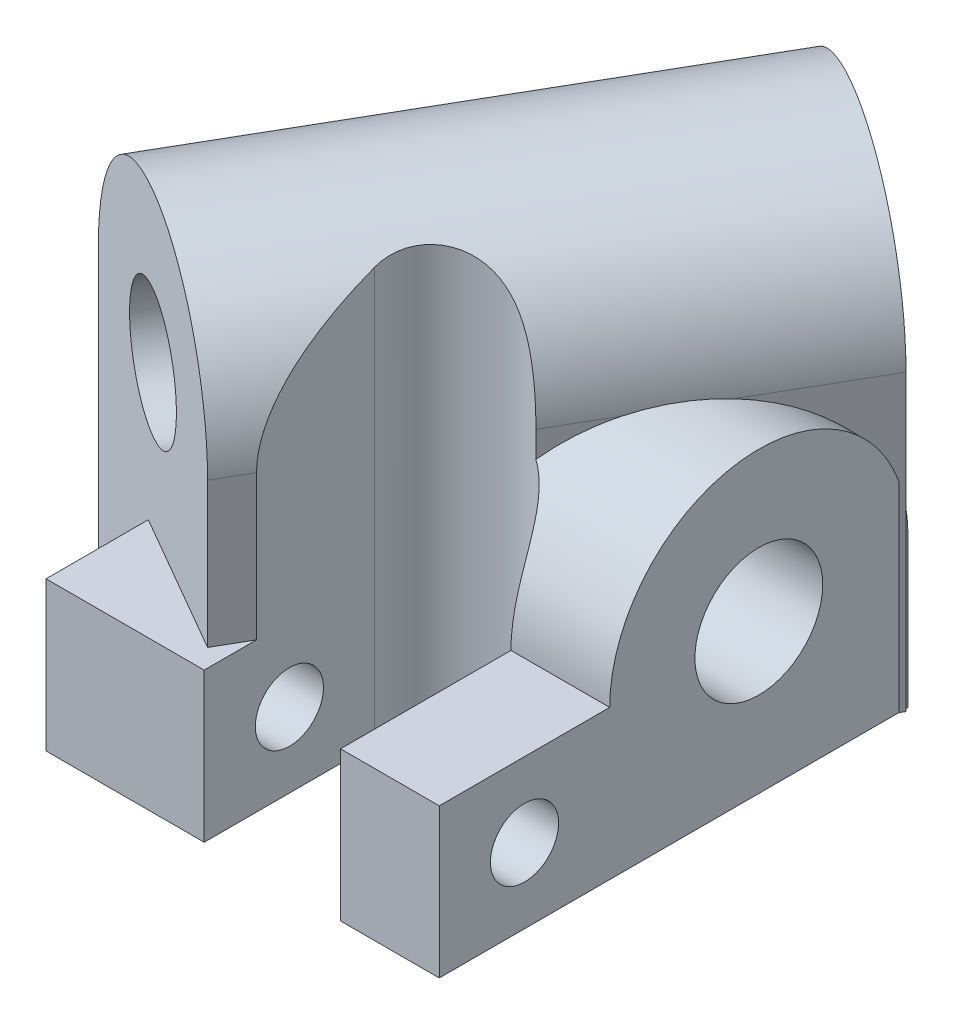
SolidWorks part; units mm, degrees
ref_plane "Front Plane" through (0, 0, 0) normal (0, 0, 1) x (1, 0, 0)
ref_plane "Top Plane" through (0, 0, 0) normal (0, 1, 0) x (1, 0, 0)
ref_plane "Right Plane" through (0, 0, 0) normal (1, 0, 0) x (0, 0, -1)
sketch "Sketch1" plane through (0, 0, 0) normal (1, 0, 0) x (0, 0, -1)
  line L0 (-8.75, 0) -> (8.75, 0)
  line L1 (8.75, 0) -> (8.75, 8.75)
  line L2 (-8.75, 8.75) -> (-8.75, 0)
  arc A0 (8.75, 8.75) -> (-8.75, 8.75) centre (0, 8.75) ccw
  circle A1 centre (0, 8.75) radius 3.75
  dimension "D1" = 8.75
  dimension "D3" = 7.5
  dimension "D2" = 5
extrude "Boss-Extrude1" add sketch "Sketch1" along normal blind 30
ref_plane "Plane1" through (-3.7889, 0, 6.5625) normal (0.5, 0, -0.866) x (-0.866, 0, -0.5)
sketch "Sketch2" plane through (-3.7889, 0, 6.5625) normal (0.5, 0, -0.866) x (-0.866, 0, -0.5)
  line L0 (-4.375, 0) -> (-4.375, 17.25)
  line L1 (-21.875, 17.25) -> (-21.875, 0)
  line L2 (-30.3558, 0) -> (-4.375, 0) construction
  line L3 (-21.875, 0) -> (-4.375, 0)
  line L4 (0, 12.5) -> (-31.5247, 12.5) construction
  arc A0 (-4.375, 17.25) -> (-21.875, 17.25) centre (-13.125, 17.25) ccw
  circle A1 centre (-13.125, 17.25) radius 3.75
  ellipse E0 centre (0, 8.75) end of major axis (0, 12.5) minor radius 1.875 construction
  ellipse E1 centre (0, 8.75) end of major axis (0, 12.5) minor radius 1.875 construction
  dimension "D1" = 8.75
  dimension "D2" = 7.5
  dimension "D3" = 1
extrude "Boss-Extrude2" add sketch "Sketch2" along normal blind 30
sketch "Sketch3" plane through (0, 0, 0) normal (0, -1, 0) x (1, 0, 0)
  line L1 (17.3205, 3.75) -> (10.8253, 15) construction
  line L3 (20.2073, 8.75) -> (15.1554, 17.5) construction
  line L4 (17.3205, 3.75) -> (30, 3.75) construction
  line L5 (30, 8.75) -> (30, -8.2115) construction
  line L6 (30, 8.75) -> (20.2073, 8.75) construction
  line L7 (-7.9566, 4.1562) -> (0.3789, 8.9687) construction
  line L8 (24.2073, 8.75) -> (24.2073, 15.6782)
  line L9 (16.2073, 15.6782) -> (24.2073, 15.6782)
  line L10 (16.2073, 15.6782) -> (16.2073, 8.75)
  arc A0 (16.2073, 8.75) -> (24.2073, 8.75) centre (20.2073, 8.75) ccw
  dimension "D1" = 8
  dimension "D2" = 5
  dimension "D3" = 5
extrude "Cut-Extrude1" cut sketch "Sketch3" against normal through all
sketch "Sketch4" plane through (0, 0, 0) normal (0, -1, 0) x (1, 0, 0)
  line L0 (24.2073, 8.75) -> (24.2073, 18.75)
  line L1 (24.2073, 18.75) -> (30, 18.75)
  line L2 (30, 18.75) -> (30, 8.75)
  line L3 (30, 8.75) -> (24.2073, 8.75)
  arc A0 (16.2073, 8.75) -> (24.2073, 8.75) centre (20.2073, 8.75) ccw construction
  arc A1 (16.2073, 8.75) -> (24.2073, 8.75) centre (20.2073, 8.75) ccw construction
  circle A2 centre (20.2073, 8.75) radius 4 construction
  dimension "D1" = 6
extrude "Boss-Extrude3" add sketch "Sketch4" against normal blind 8.75
sketch "Sketch6" plane through (0, 0, 0) normal (0, -1, 0) x (1, 0, 0)
  line L0 (16.2073, 15.6782) -> (16.2073, 18.75)
  line L1 (16.2073, 18.75) -> (6.9282, 18.75)
  line L2 (6.9282, 18.75) -> (6.9282, 12.75)
  line L3 (15.1554, 17.5) -> (0, 8.75) construction
  line L4 (30, 18.75) -> (24.2073, 18.75) construction
  line L5 (6.9282, 12.75) -> (16.2073, 15.6782)
  dimension "D1" = 6
extrude "Boss-Extrude4" add sketch "Sketch6" against normal up to surface (8.75 mm away) up to face at (27.1036, 8.75, 13.75)
sketch "Sketch5" plane through (30, 0, 0) normal (1, 0, 0) x (0, 0, -1)
  line L0 (-14.9644, 4.375) -> (-9.1409, 4.375) construction
  line L1 (-8.75, 8.75) -> (-18.75, 8.75) construction
  line L3 (-15.3741, 8.75) -> (-10.3407, 8.75) construction
  line L4 (-14.9644, 0) -> (-9.931, 0) construction
  line L5 (-18.75, 0) -> (8.2115, 0) construction
  line L6 (-18.75, 8.75) -> (-18.75, 0) construction
  circle A0 centre (-13.75, 4.375) radius 2
  dimension "D1" = 4
  dimension "D2" = 5
extrude "Cut-Extrude2" cut sketch "Sketch5" against normal through all
sketch "Sketch7" plane through (0, 0, 0) normal (-1, 0, 0) x (0, 0, 1)
  circle A0 centre (0, 8.75) radius 3.75 construction
  circle A1 centre (0, 8.75) radius 3.75
extrude "Cut-Extrude3" cut sketch "Sketch7" against normal through all
sketch "Sketch8" plane through (-3.7889, 0, 6.5625) normal (-0.5, 0, 0.866) x (0.866, 0, 0.5)
  circle A0 centre (13.125, 17.25) radius 3.75 construction
  circle A1 centre (13.125, 17.25) radius 3.75
extrude "Cut-Extrude4" cut sketch "Sketch8" against normal through all
